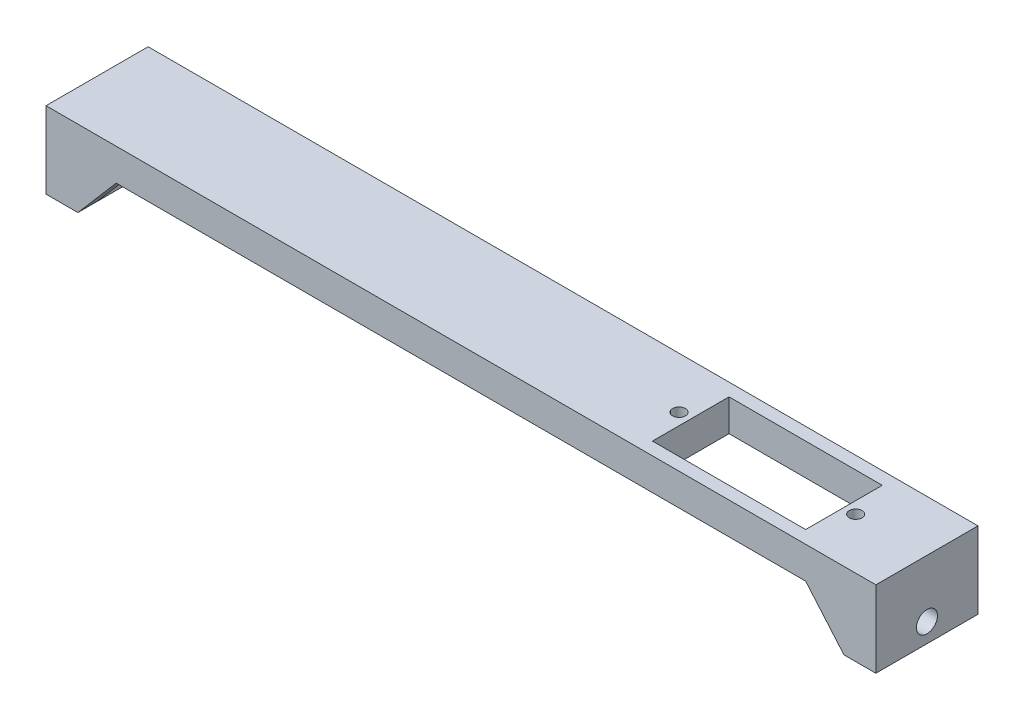
SolidWorks part; units mm, degrees
ref_plane "前视基准面" through (0, 0, 0) normal (0, 0, 1) x (1, 0, 0)
ref_plane "上视基准面" through (0, 0, 0) normal (0, 1, 0) x (1, 0, 0)
ref_plane "右视基准面" through (0, 0, 0) normal (1, 0, 0) x (0, 0, -1)
sketch "草图1" plane through (0, 0, 0) normal (0, 0, 1) x (1, 0, 0)
  line L0 (-65, 0) -> (65, 0)
  line L1 (65, 0) -> (65, -12)
  line L2 (65, -12) -> (60, -12)
  line L3 (60, -12) -> (60, -5)
  line L4 (60, -5) -> (-60, -5)
  line L5 (-60, -5) -> (-60, -12)
  line L6 (-60, -12) -> (-65, -12)
  line L7 (-65, -12) -> (-65, 0)
  line L8 (0, -7.4248) -> (0, 9.2484) construction
  dimension "D1" = 5
  dimension "D2" = 5
  dimension "D3" = 130
  dimension "D4" = 12
  dimension "D5" = 12
extrude "凸台-拉伸2" add sketch "草图1" along normal blind 16
sketch "草图3" plane through (-60, 0, 0) normal (1, 0, 0) x (0, 0, -1)
  line L0 (0, 0) -> (0, -12) construction
  line L1 (-16, -12) -> (0, -12) construction
  circle A0 centre (-8, -9) radius 1.65
  dimension "D2" = 3.3
  dimension "D1" = 3
  dimension "D3" = 8
extrude "切除-拉伸1" cut sketch "草图3" against normal through all both and the other way through all
sketch "草图4" plane through (0, 0, 0) normal (0, 0, -1) x (-1, 0, 0)
  line L0 (54, -5) -> (60, -12)
  line L1 (60, -5) -> (-60, -5) construction
  line L2 (54, -5) -> (60, -5)
  line L4 (60, -5) -> (60, -12)
  dimension "D1" = 6
extrude "凸台-拉伸3" add sketch "草图4" against normal blind 3
sketch "草图5" plane through (0, -5, 0) normal (0, -1, 0) x (1, 0, 0)
  line L0 (60, 8) -> (-60, 8) construction
  line L1 (60, 16) -> (60, 0) construction
  line L2 (-60, 16) -> (-60, 3) construction
ref_plane "基准面3" through (0, 0, 8) normal (0, 0, 1) x (1, 0, 0)
mirror "镜向1" about plane through (0, 0, 8) normal (0, 0, 1) of "凸台-拉伸3"
sketch "草图6" plane through (0, 0, 0) normal (0, 1, 0) x (1, 0, 0)
  line L0 (0, -16) -> (0, 0) construction
  line L1 (65, -16) -> (-65, -16) construction
mirror "镜向2" about plane through (0, 0, 0) normal (1, 0, 0) of "镜向1", "凸台-拉伸3"
sketch "草图7" plane through (0, -5, 0) normal (0, -1, 0) x (1, 0, 0)
  line L0 (60, 8) -> (-60, 8) construction
  line L1 (52, 2) -> (28, 2)
  line L2 (52, 2) -> (52, 14)
  line L3 (52, 14) -> (28, 14)
  line L4 (28, 2) -> (28, 14)
  line L5 (52, 2) -> (28, 14) construction
  line L6 (52, 14) -> (28, 2) construction
  line L8 (65, 16) -> (65, 0) construction
  point P0 (40, 8)
  dimension "D1" = 12
  dimension "D2" = 24
  dimension "D3" = 25
extrude "切除-拉伸2" cut sketch "草图7" against normal blind 5 contours L1 L4 L3 L2
sketch "草图10" plane through (0, -5, 0) normal (0, -1, 0) x (1, 0, 0)
  line L0 (40, 14) -> (40, 2) construction
  line L1 (52, 14) -> (28, 14) construction
  line L2 (52, 2) -> (28, 2) construction
  line L3 (65, 16) -> (-65, 16) construction
  circle A0 centre (53.835, 8) radius 1
  circle A1 centre (26.165, 8) radius 1
  point P10 (40, 8)
  dimension "D2" = 2
  dimension "D3" = 8
  dimension "D1" = 13.835
extrude "切除-拉伸3" cut sketch "草图10" against normal blind 5
